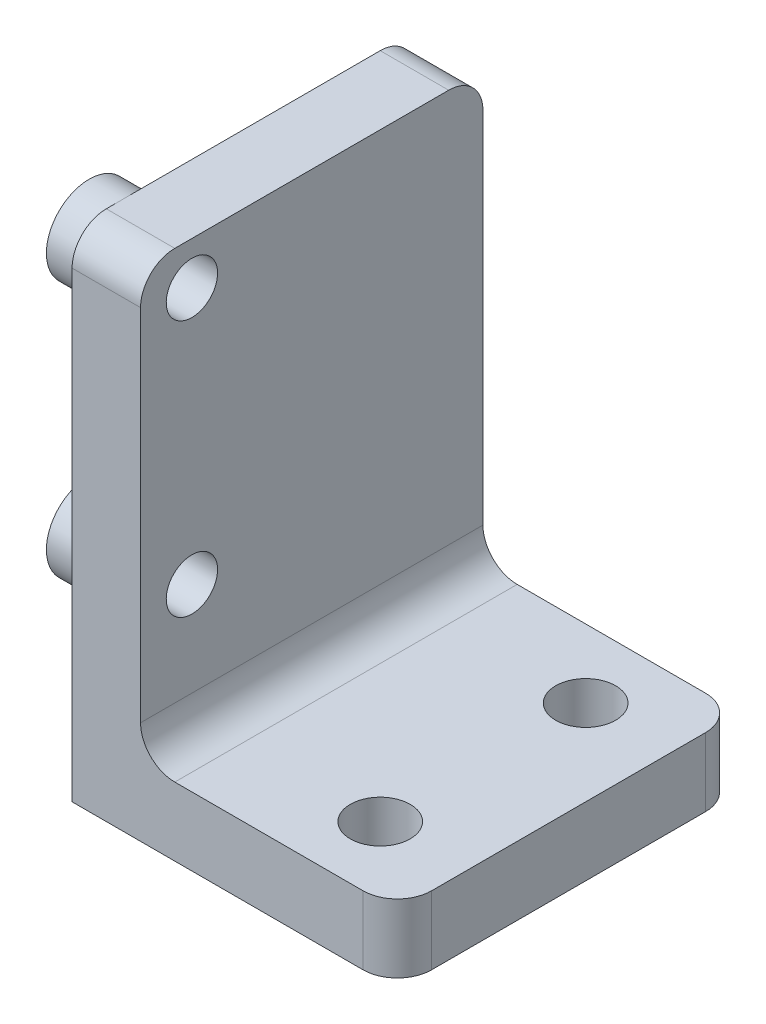
SolidWorks part; units mm, degrees
ref_plane "Front Plane" through (0, 0, 0) normal (0, 0, 1) x (1, 0, 0)
ref_plane "Top Plane" through (0, 0, 0) normal (0, 1, 0) x (1, 0, 0)
ref_plane "Right Plane" through (0, 0, 0) normal (1, 0, 0) x (0, 0, -1)
sketch "Sketch1" plane through (0, 0, 0) normal (0, 0, 1) x (1, 0, 0)
  line L0 (0, 0) -> (0, 29)
  line L1 (0, 29) -> (4, 29)
  line L2 (4, 29) -> (4, 4)
  line L3 (4, 4) -> (19, 4)
  line L4 (19, 4) -> (19, 0)
  line L5 (19, 0) -> (0, 0)
  dimension "D1" = 4
  dimension "D2" = 4
  dimension "D3" = 25
  dimension "D4" = 15
extrude "Boss-Extrude1" add sketch "Sketch1" along normal blind 20
sketch "Sketch2" plane through (0, 0, 0) normal (-1, 0, 0) x (0, 0, 1)
  line L0 (20, 29) -> (0, 29) construction
  line L1 (20, 29) -> (20, 0) construction
  circle A0 centre (17, 26.5) radius 1.5
  circle A1 centre (17, 11.5) radius 1.5
  dimension "D2" = 3
  dimension "D1" = 15
  dimension "D3" = 2.5
  dimension "D4" = 3
extrude "Cut-Extrude1" cut sketch "Sketch2" against normal through all
sketch "Sketch3" plane through (0, 4, 0) normal (0, 1, 0) x (1, 0, 0)
  line L0 (19, -20) -> (19, 0) construction
  circle A0 centre (14, -4) radius 1.75
  circle A1 centre (14, -16) radius 1.75
  point P6 (19, -10)
  dimension "D1" = 3.5
  dimension "D2" = 3.5
  dimension "D3" = 12
  dimension "D4" = 6
  dimension "D5" = 5
extrude "Cut-Extrude2" cut sketch "Sketch3" against normal through all
fillet "Fillet1" radius 2 5 edges at (19, 2, 0) (19, 2, 20) (4, 4, 10) (2, 29, 0) (2, 29, 20)
sketch "Sketch4" plane through (4, 0, 0) normal (1, 0, 0) x (0, 0, -1)
  line L0 (-18, 29) -> (-2, 29) construction
  circle A0 centre (-17, 26.5) radius 2.5
  circle A1 centre (-17, 11.5) radius 2.5
  circle A2 centre (-17, 11.5) radius 1.5 construction
  circle A3 centre (-17, 26.5) radius 1.5 construction
  circle A4 centre (-17, 11.5) radius 1.5
  circle A5 centre (-17, 26.5) radius 1.5
extrude "Boss-Extrude2" add sketch "Sketch4" against normal blind 2 from surface at -4 starting at face at (0, 25, 17)
